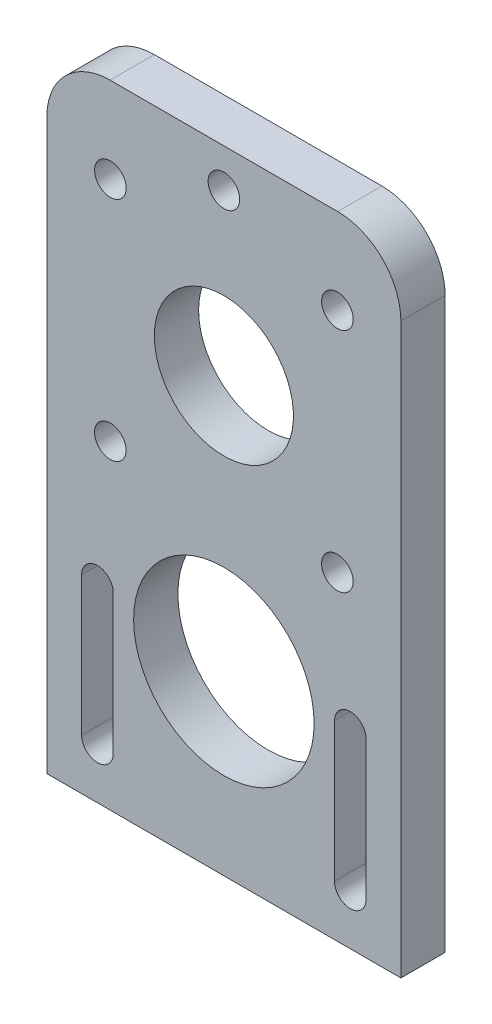
SolidWorks part; units mm, degrees
ref_plane "Front Plane" through (0, 0, 0) normal (0, 0, 1) x (1, 0, 0)
ref_plane "Top Plane" through (0, 0, 0) normal (0, 1, 0) x (1, 0, 0)
ref_plane "Right Plane" through (0, 0, 0) normal (1, 0, 0) x (0, 0, -1)
sketch "Sketch1" plane through (0, 0, 0) normal (0, 0, 1) x (1, 0, 0)
  line L1 (0, 0) -> (56, 0)
  line L2 (0, 0) -> (0, 100)
  line L3 (0, 100) -> (56, 100)
  line L4 (56, 0) -> (56, 100)
  dimension "D1" = 56
  dimension "D2" = 100
extrude "Boss-Extrude1" add sketch "Sketch1" along normal blind 7 contours L3 L4 L1 L2
sketch "Sketch2" plane through (0, 0, 7) normal (0, 0, 1) x (1, 0, 0)
  line L0 (28, 100) -> (28, 0) construction
  line L1 (0, 100) -> (56, 100) construction
  line L2 (0, 0) -> (56, 0) construction
  line L3 (0, 50) -> (56, 50) construction
  line L4 (0, 0) -> (0, 100) construction
  line L5 (56, 0) -> (56, 100) construction
  line L6 (8, 30) -> (8, 8) construction
  line L7 (10.5, 30) -> (10.5, 8)
  line L8 (5.5, 30) -> (5.5, 8)
  line L9 (48, 30) -> (48, 8) construction
  line L10 (50.5, 30) -> (50.5, 8)
  line L11 (45.5, 30) -> (45.5, 8)
  circle A0 centre (28, 28) radius 14.275
  arc A5 (10.5, 30) -> (5.5, 30) centre (8, 30) ccw
  arc A6 (5.5, 8) -> (10.5, 8) centre (8, 8) ccw
  arc A7 (50.5, 30) -> (45.5, 30) centre (48, 30) ccw
  arc A8 (45.5, 8) -> (50.5, 8) centre (48, 8) ccw
  point P22 (8, 19)
  point P27 (48, 19)
  dimension "D1" = 28.55
  dimension "D6" = 8
  dimension "D7" = 70
  dimension "D8" = 8
  dimension "D9" = 8
  dimension "D10" = 8
  dimension "D11" = 8
  dimension "D12" = 70
  dimension "D13" = 8
  dimension "D14" = 5
  dimension "D15" = 5
extrude "Cut-Extrude1" cut sketch "Sketch2" against normal through all
sketch "Sketch3" plane through (0, 0, 0) normal (0, 0, -1) x (-1, 0, 0)
  line L1 (0, 0) -> (0, 100) construction
  line L4 (0, 100) -> (-56, 100) construction
  circle A1 centre (-28, 68.5) radius 11
  circle A2 centre (-28, 28) radius 14.275 construction
  point P13 (-28, 100)
  dimension "D3" = 40.5
  dimension "D1" = 22
  dimension "D2" = 28
extrude "Cut-Extrude2" cut sketch "Sketch3" against normal blind 10
sketch "Sketch4" plane through (0, 0, 0) normal (0, 0, -1) x (-1, 0, 0)
  circle A0 centre (-45.966, 86.455) radius 2.5
  circle A1 centre (-28.0077, 93.9) radius 2.5
  circle A2 centre (-10.045, 86.466) radius 2.5
  circle A4 centre (-45.955, 50.534) radius 2.5
  circle A5 centre (-10.034, 50.545) radius 2.5
  dimension "D1" = 5
  dimension "D2" = 5
  dimension "D3" = 5
  dimension "D4" = 5
  dimension "D5" = 5
extrude "Cut-Extrude3" cut sketch "Sketch4" against normal through all
fillet "Fillet1" radius 10 2 edges at (56, 100, 3.5) (0, 100, 3.5)
